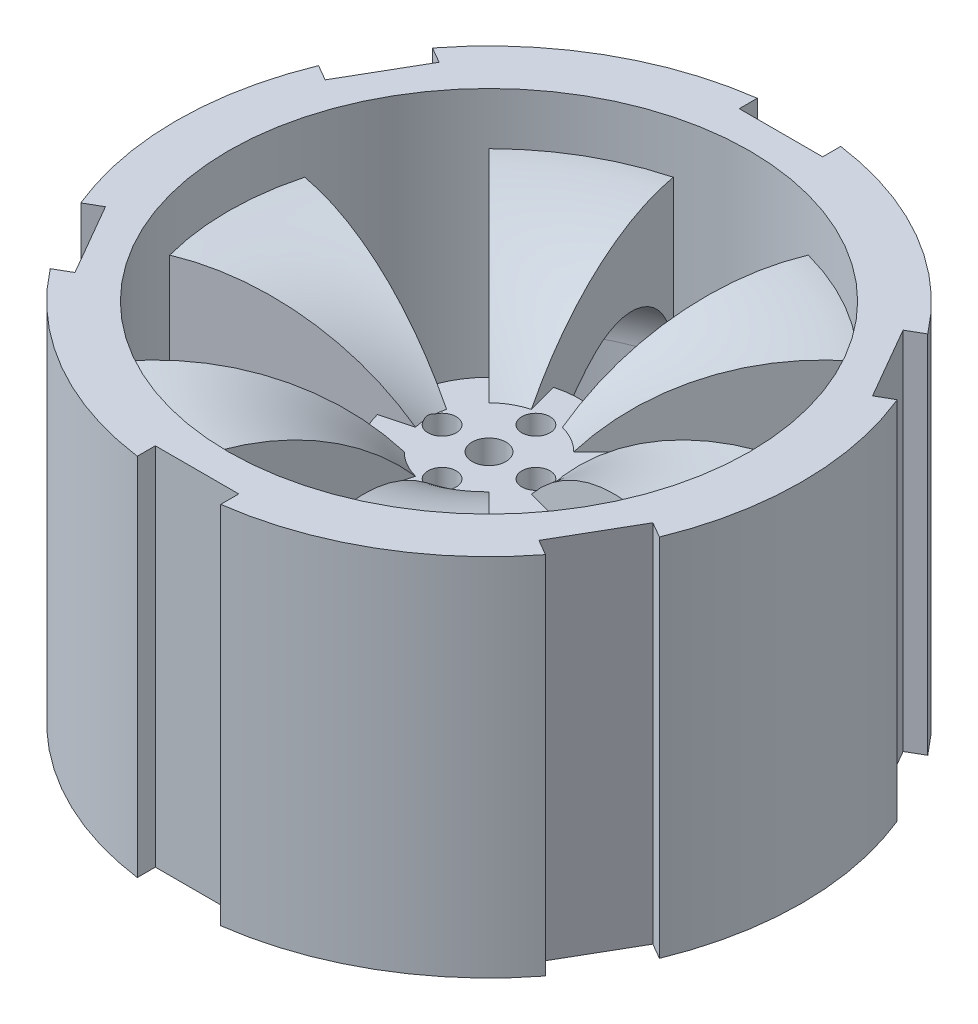
SolidWorks part; units mm, degrees
material "ABS"
ref_plane "Front Plane" through (0, 0, 0) normal (0, 0, 1) x (1, 0, 0)
ref_plane "Top Plane" through (0, 0, 0) normal (0, 1, 0) x (1, 0, 0)
ref_plane "Right Plane" through (0, 0, 0) normal (1, 0, 0) x (0, 0, -1)
sketch "Sketch1" plane through (0, 0, 0) normal (0, 1, 0) x (1, 0, 0)
  circle A0 centre (0, 0) radius 17.5
  dimension "D1" = 35
extrude "Boss-Extrude1" add sketch "Sketch1" along normal mid plane 20
sketch "Sketch3" plane through (0, 0, 0) normal (0, 1, 0) x (1, 0, 0)
  circle A0 centre (0, 0) radius 60
  circle A1 centre (0, 0) radius 50
  dimension "D1" = 120
  dimension "D2" = 10
extrude "Boss-Extrude2" add sketch "Sketch3" along normal mid plane 70
ref_axis "Axis1" through (0, 10, 0) along (0, -1, 0)
sketch "Sketch4" plane through (0, 0, 0) normal (0, 0, 1) x (1, 0, 0)
  line L0 (17.5, 10) -> (-17.5, 10) construction
  line L1 (-50, 35) -> (-50, -35) construction
  line L2 (-17.5, 10) -> (-17.5, -10) construction
  line L3 (-11.5, 10) -> (-17.5, 10)
  line L4 (-17.5, 10) -> (-17.5, 0)
  line L5 (-50, 25) -> (-50, 10)
  line L7 (50, 35) -> (-50, 35) construction
  arc A1 (-11.5, 10) -> (-50, 25) centre (-45.263, -19.75) ccw
  arc A2 (-17.5, 0) -> (-50, 10) centre (-41.019, -18.6241) ccw
  dimension "D1" = 15
  dimension "D4" = 60
  dimension "D5" = 45
  dimension "D2" = 10
  dimension "D3" = 6
revolve "Revolve1" add sketch "Sketch4" angle 30 mid plane about axis through (0, 10, 0) along (0, -1, 0)
pattern_circular "CirPattern1" count 6 over 360 about axis through (0, 0, 0) along (0, 1, 0) of "Revolve1"
sketch "Sketch5" plane through (0, 10, 0) normal (0, 1, 0) x (1, 0, 0)
  circle A0 centre (0, 0) radius 3.25
  circle A1 centre (0, 9) radius 2.7
  circle A2 centre (9, 0) radius 2.7
  circle A3 centre (0, -9) radius 2.7
  circle A4 centre (-9, 0) radius 2.7
  point P14 (0, 0)
  dimension "D1" = 6.5
  dimension "D3" = 5.4
  dimension "D2" = 9
  dimension "D4" = 4
extrude "Cut-Extrude1" cut sketch "Sketch5" against normal mid plane 70
fillet "Fillet1" radius 15 6 edges at (25, 10, 43.3013) (-25, 10, 43.3013) (-50, 10, 0) (-25, 10, -43.3013) (25, 10, -43.3013) (50, 10, 0)
sketch "Sketch6" plane through (0, 35, 0) normal (0, 1, 0) x (1, 0, 0)
  line L0 (0, 0) -> (0, 65.4375) construction
  line L2 (-8, 56) -> (8, 56)
  line L3 (-8, 56) -> (-8, 64)
  line L4 (-8, 64) -> (8, 64)
  line L5 (8, 56) -> (8, 64)
  line L6 (-8, 56) -> (8, 64) construction
  line L7 (-8, 64) -> (8, 56) construction
  circle A0 centre (0, 0) radius 60 construction
  point P3 (0, 60)
  dimension "D1" = 8
  dimension "D2" = 16
extrude "Cut-Extrude2" cut sketch "Sketch6" against normal blind 79
pattern_circular "CirPattern2" count 6 over 360 about axis through (0, 0, 0) along (0, 1, 0) of "Cut-Extrude2"
